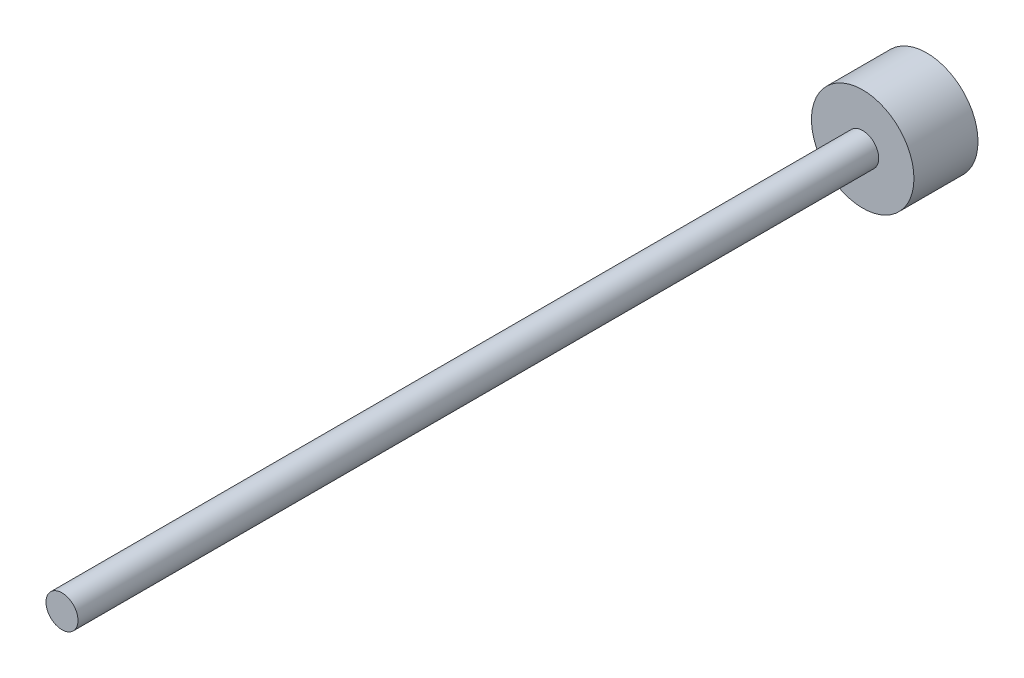
SolidWorks part; units mm, degrees
material "合金钢"
ref_plane "前视基准面" through (0, 0, 0) normal (0, 0, 1) x (1, 0, 0)
ref_plane "上视基准面" through (0, 0, 0) normal (0, 1, 0) x (1, 0, 0)
ref_plane "右视基准面" through (0, 0, 0) normal (1, 0, 0) x (0, 0, -1)
sketch "草图1" plane through (0, 0, 0) normal (0, 0, 1) x (1, 0, 0)
  circle A0 centre (0, 0) radius 8
extrude "凸台-拉伸1" add sketch "草图1" along normal blind 10
sketch "草图2" plane through (0, 0, 10) normal (0, 0, 1) x (1, 0, 0)
  circle A0 centre (0, 0) radius 2.5
extrude "凸台-拉伸2" add sketch "草图2" along normal blind 125
